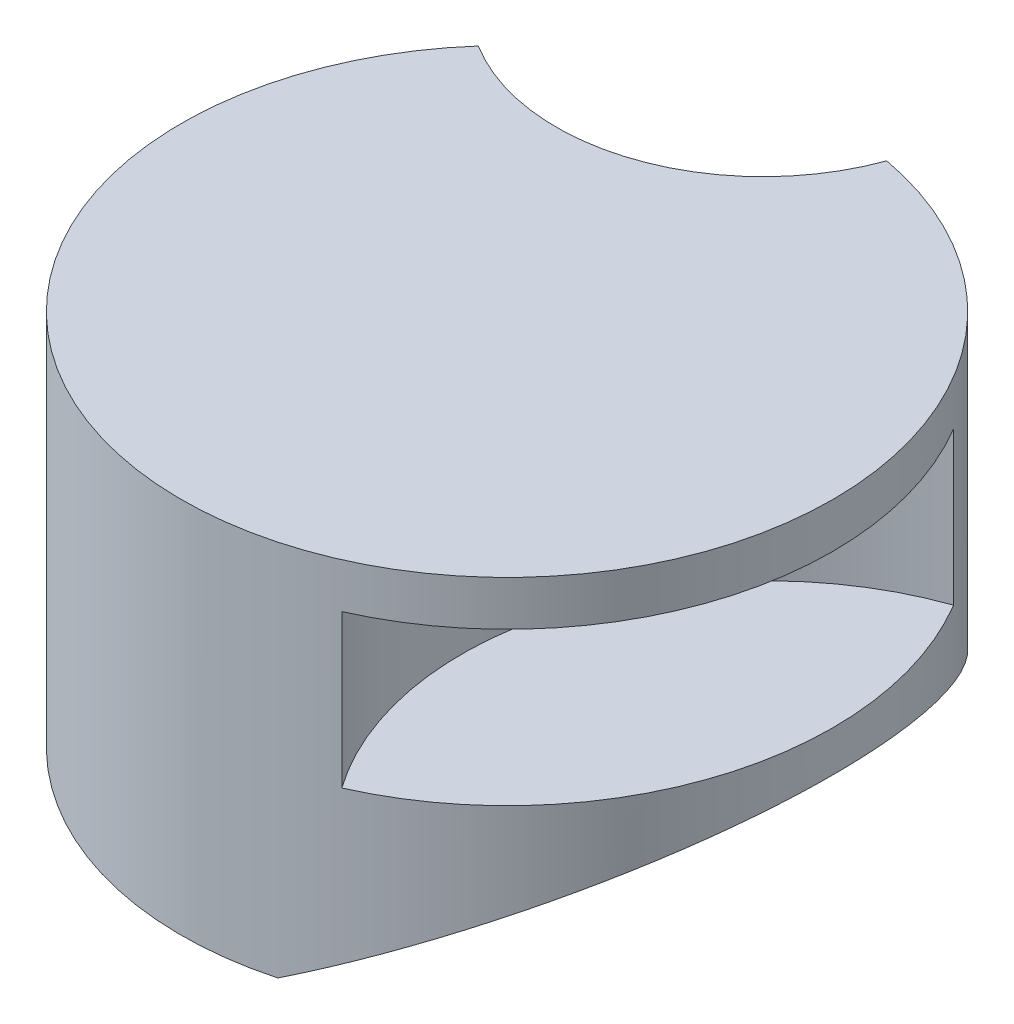
SolidWorks part; units mm, degrees
ref_plane "Front Plane" through (0, 0, 0) normal (0, 0, 1) x (1, 0, 0)
ref_plane "Top Plane" through (0, 0, 0) normal (0, 1, 0) x (1, 0, 0)
ref_plane "Right Plane" through (0, 0, 0) normal (1, 0, 0) x (0, 0, -1)
sketch "Sketch1" plane through (0, 0, 0) normal (0, 1, 0) x (1, 0, 0)
  arc A0 (-54.3552, 47.9766) -> (13.2314, 71.2824) centre (0, 0) ccw
  arc A1 (-54.3552, 47.9766) -> (13.2314, 71.2824) centre (-30, 87) ccw
  point P4 (0, 0)
  dimension "D1" = 30
  dimension "D2" = 72.5
  dimension "D3" = 46
  dimension "D4" = 87
extrude "Boss-Extrude1" add sketch "Sketch1" along normal blind 84
sketch "Sketch2" plane through (0, 84, 0) normal (0, 1, 0) x (1, 0, 0)
  arc A0 (62.2908, 37.096) -> (29.4657, -66.2421) centre (85, -27) ccw
  arc A1 (62.2908, 37.096) -> (29.4657, -66.2421) centre (0, 0) cw
  arc A2 (-54.3552, 47.9766) -> (13.2314, 71.2824) centre (0, 0) ccw construction
  point P1 (0, 0)
  point P6 (0, 0)
  dimension "D1" = 68
  dimension "D4" = 72.5
  dimension "D2" = 27
  dimension "D3" = 85
ref_plane "Plane1" through (0, 74, 0) normal (0, 1, 0) x (1, 0, 0)
sketch "Sketch3" plane through (0, 74, 0) normal (0, 1, 0) x (1, 0, 0)
  arc A0 (62.2908, 37.096) -> (29.4657, -66.2421) centre (85, -27) ccw
  arc A1 (62.2908, 37.096) -> (29.4657, -66.2421) centre (0, 0) cw
  arc A2 (29.4657, -66.2421) -> (62.2908, 37.096) centre (0, 0) ccw construction
  point P4 (0, 0)
  point P8 (0, 0)
  dimension "D3" = 72.5
  dimension "D4" = 68
  dimension "D1" = 27
  dimension "D2" = 85
extrude "Cut-Extrude2" cut sketch "Sketch3" against normal blind 34
sketch "Sketch8" plane through (0, 84, 0) normal (0, 1, 0) x (1, 0, 0)
  line L0 (0, 0) -> (0, 72.3228) construction
  circle A0 centre (0, 0) radius 72.3228
ref_plane "Plane3" through (0, 0, 72.5) normal (0, 0, 1) x (1, 0, 0)
sketch "Sketch9" plane through (0, 0, 72.5) normal (0, 0, 1) x (1, 0, 0)
  line L0 (72.5, 30.9084) -> (18.9651, 0)
  line L1 (72.5, 0) -> (72.5, 40) construction
  line L2 (-72.5, 0) -> (72.5, 0) construction
  line L3 (18.9651, 0) -> (72.5, 0)
  line L4 (72.5, 0) -> (72.5, 30.9084)
  dimension "D1" = 30
  dimension "D2" = 18.9651
extrude "Cut-Extrude3" cut sketch "Sketch9" against normal through all
ref_plane "Plane4" through (0, 63, 0) normal (0, 1, 0) x (1, 0, 0)
sketch "Sketch10" plane through (0, 63, 0) normal (0, 1, 0) x (1, 0, 0)
  line L1 (-3.3664, -32.2705) -> (7.5317, 1.2705)
  line L2 (7.5317, 1.2705) -> (-21, 22)
  line L3 (-21, 22) -> (-49.5317, 1.2705)
  line L4 (-49.5317, 1.2705) -> (-38.6336, -32.2705)
  line L5 (-38.6336, -32.2705) -> (-3.3664, -32.2705)
  circle A0 centre (-21, -8) radius 30 construction
  dimension "D1" = 8
  dimension "D2" = 21
  dimension "D3" = 30
extrude "Cut-Extrude4" cut sketch "Sketch10" against normal blind 43
